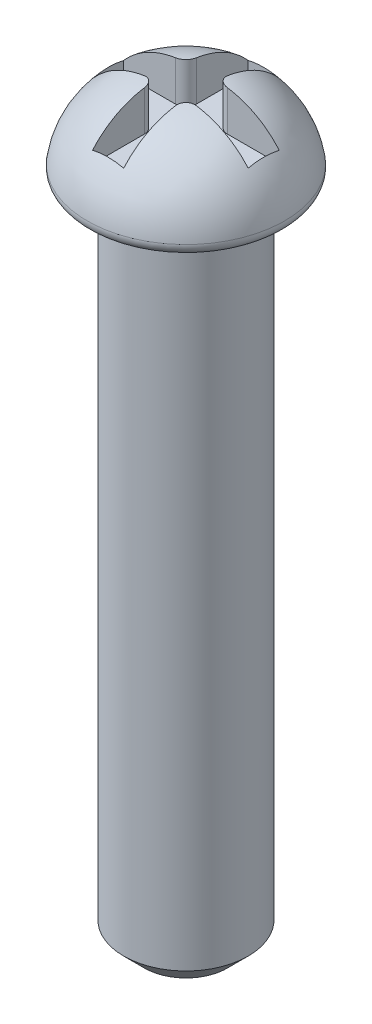
SolidWorks part; units mm, degrees
material "Alloy Steel"
ref_plane "Front Plane" through (0, 0, 0) normal (0, 0, 1) x (1, 0, 0)
ref_plane "Top Plane" through (0, 0, 0) normal (0, 1, 0) x (1, 0, 0)
ref_plane "Right Plane" through (0, 0, 0) normal (1, 0, 0) x (0, 0, -1)
sketch "Sketch1" plane through (0, 0, 0) normal (0, 0, 1) x (1, 0, 0)
  line L0 (0, 0) -> (-1.5, 0)
  line L1 (-1.5, 0) -> (-1.5, 15.75)
  line L2 (-1.75, 16) -> (-2.1324, 16)
  line L3 (0, 0) -> (0, 18)
  arc A2 (-2.3799, 16.285) -> (0, 18) centre (-0.3667, 16) cw
  arc A3 (-1.5, 15.75) -> (-1.75, 16) centre (-1.75, 15.75) ccw
  arc A4 (-2.1324, 16) -> (-2.3799, 16.285) centre (-2.1324, 16.25) cw
  point P13 (-1.5, 16)
  point P16 (-2.4, 16)
  dimension "D2" = 16
  dimension "D5" = 0.25
  dimension "D1" = 18
  dimension "D3" = 1.5
  dimension "D4" = 2.4
revolve "Revolve1" add sketch "Sketch1" angle 360 about L3
chamfer "Chamfer1" distance 0.5 angle 45 1 edges at (0, 0, -1.5)
thread "Thread2" [suppressed] pitch 0.5 start angle 0, offset 0, length 0, pitch 0.5, diameter 3
ref_plane "Plane2" through (-1.5, 15.75, 0) normal (0, 0, 1) x (-1, 0, 0)
sketch "Thread Profile2" plane through (-1.5, 15.75, 0) normal (0, 0, 1) x (-1, 0, 0)
  line L0 (0, 0) -> (0, 0.5) construction
  line L11 (0, 0) -> (0, 0.4375)
  line L12 (0, 0.4375) -> (-0.2706, 0.2812)
  line L13 (-0.2706, 0.2812) -> (-0.2706, 0.1562)
  line L15 (-0.2706, 0.1562) -> (0, 0)
  line L17 (-0.2706, 0.2187) -> (0, 0.2187) construction
  point P2 (0, 0)
  dimension "Pitch" = 0.5
  dimension "Profile_Angle" = 60
  dimension "Profile_Land" = 0.125
  dimension "Profile_Height" = 0.2706
sketch "Sketch7" [suppressed] plane through (0, 0, 0) normal (0, 0, -1) x (-1, 0, 0)
  line L4 (1.5, 15.75) -> (1.2294, 15.5938)
  line L5 (1.2294, 15.5938) -> (1.2294, 15.4688)
  line L6 (1.2294, 15.4688) -> (1.5, 15.3125)
  line L7 (1.5, 15.3125) -> (1.5, 15.75)
  line L8 (1.5, 15.75) -> (1.2294, 15.5938)
  line L9 (1.2294, 15.5938) -> (1.2294, 15.4688)
  line L10 (1.2294, 15.4688) -> (1.5, 15.3125)
  line L11 (1.5, 15.3125) -> (1.5, 15.75)
  dimension "D1" = 0
extrude "Cut-Extrude2" [suppressed] cut sketch "Sketch7" against normal through all
sketch3d "3DSketch1" plane through (0, 0, 0) normal (0, 0, 1) x (1, 0, 0)
sketch "Sketch9" plane through (0, 18.0333, 0) normal (0, 1, 0) x (1, 0, 0)
  line L0 (0, 2.0901) -> (0, -2.2) construction
  line L1 (-2.3463, 0) -> (2.2803, 0) construction
  line L2 (-0.375, 1.875) -> (0.375, 1.875)
  line L3 (0.375, 1.875) -> (0.375, 0.625)
  line L4 (0.625, 0.375) -> (1.875, 0.375)
  line L5 (1.875, 0.375) -> (1.875, -0.375)
  line L6 (1.875, -0.375) -> (0.625, -0.375)
  line L7 (0.375, -0.625) -> (0.375, -1.875)
  line L8 (0.375, -1.875) -> (-0.375, -1.875)
  line L9 (-0.375, -1.875) -> (-0.375, -0.625)
  line L10 (-0.625, -0.375) -> (-1.875, -0.375)
  line L11 (-1.875, -0.375) -> (-1.875, 0.375)
  line L12 (-1.875, 0.375) -> (-0.625, 0.375)
  line L13 (-0.375, 0.625) -> (-0.375, 1.875)
  arc A0 (-0.375, -0.625) -> (-0.625, -0.375) centre (-0.625, -0.625) ccw
  arc A1 (0.625, -0.375) -> (0.375, -0.625) centre (0.625, -0.625) ccw
  arc A2 (0.375, 0.625) -> (0.625, 0.375) centre (0.625, 0.625) ccw
  arc A3 (-0.625, 0.375) -> (-0.375, 0.625) centre (-0.625, 0.625) ccw
  point P21 (0.375, -0.375)
  point P24 (0.375, 0.375)
  point P27 (-0.375, 0.375)
  dimension "D5" = 0.25
  dimension "D1" = 0.75
  dimension "D2" = 0.75
  dimension "D3" = 1.5
  dimension "D4" = 1.5
extrude "Cut-Extrude3" cut sketch "Sketch9" against normal blind 1
